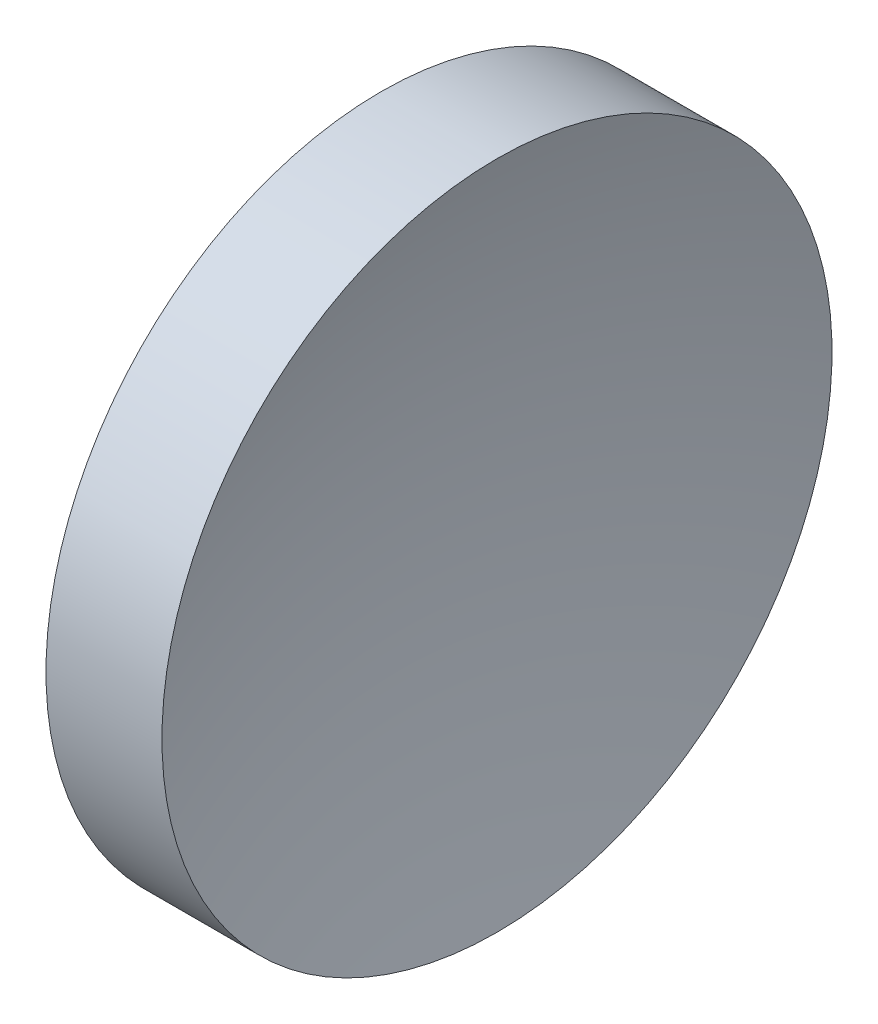
SolidWorks part; units mm, degrees
ref_plane "前视基准面" through (0, 0, 0) normal (0, 0, 1) x (1, 0, 0)
ref_plane "上视基准面" through (0, 0, 0) normal (0, 1, 0) x (1, 0, 0)
ref_plane "右视基准面" through (0, 0, 0) normal (1, 0, 0) x (0, 0, -1)
sketch "草图1" plane through (0, 0, 0) normal (0, 0, 1) x (1, 0, 0)
  line L0 (43.012, 26.0623) -> (51.5611, 26.0623) construction
  line L1 (44.8544, 26.0623) -> (44.8544, 34.0623)
  line L2 (44.8544, 34.0623) -> (47.624, 34.0623)
  line L3 (46.3544, 26.0623) -> (44.8544, 26.0623)
  arc A0 (47.624, 34.0623) -> (46.3544, 26.0623) centre (72.1944, 26.0623) ccw
revolve "旋转1" add sketch "草图1" angle 360 about L0
